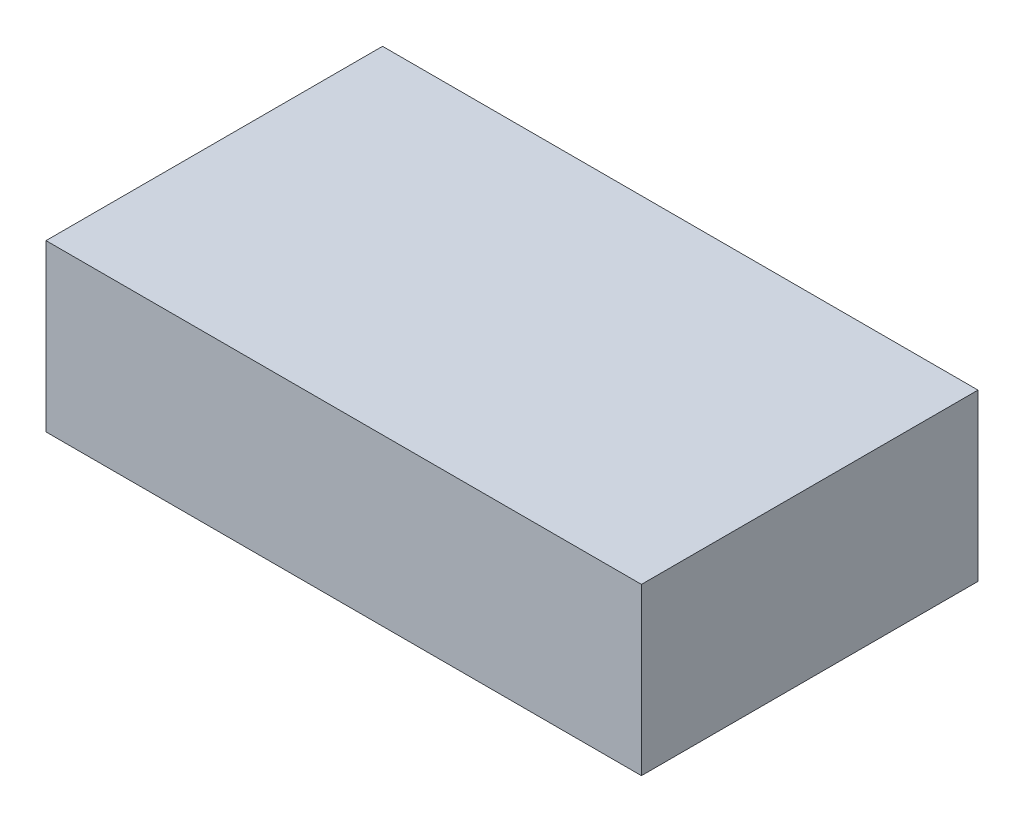
SolidWorks part; units mm, degrees
ref_plane "Front Plane" through (0, 0, 0) normal (0, 0, 1) x (1, 0, 0)
ref_plane "Top Plane" through (0, 0, 0) normal (0, 1, 0) x (1, 0, 0)
ref_plane "Right Plane" through (0, 0, 0) normal (1, 0, 0) x (0, 0, -1)
sketch "Sketch1" plane through (0, 0, 0) normal (0, 1, 0) x (1, 0, 0)
  line L1 (-55.9317, -22.274) -> (59.0683, -22.274)
  line L2 (-55.9317, -22.274) -> (-55.9317, 42.726)
  line L3 (-55.9317, 42.726) -> (59.0683, 42.726)
  line L4 (59.0683, -22.274) -> (59.0683, 42.726)
  dimension "D1" = 65
  dimension "D2" = 115
extrude "Boss-Extrude1" add sketch "Sketch1" along normal blind 32
